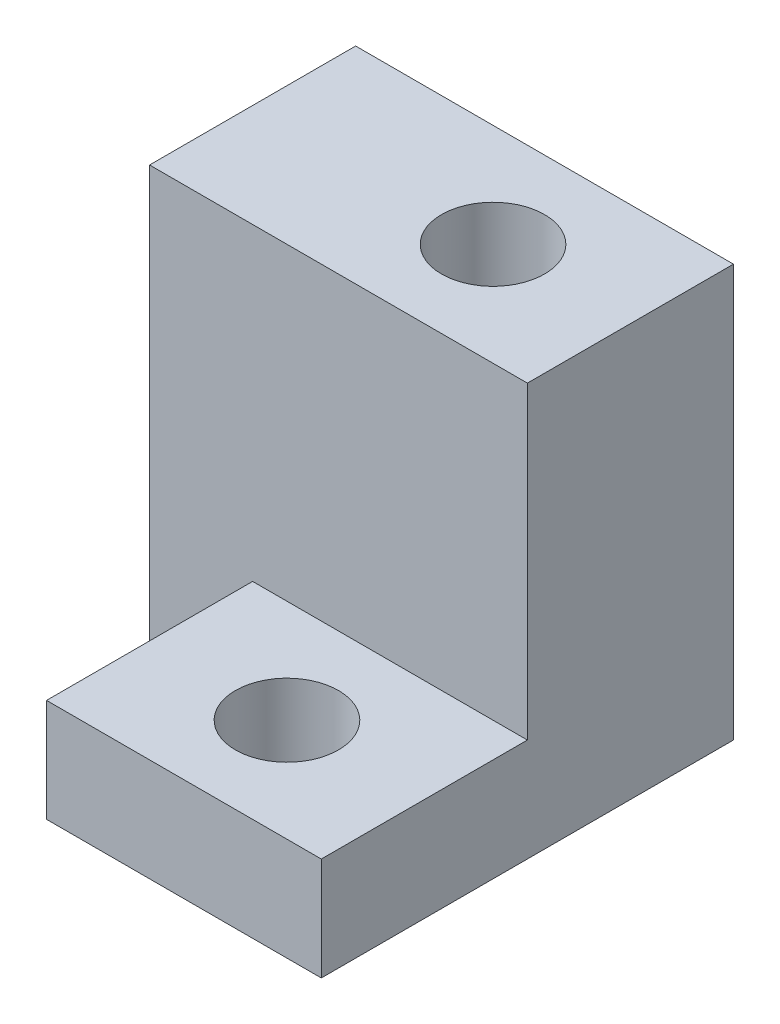
SolidWorks part; units mm, degrees
ref_plane "Front Plane" through (0, 0, 0) normal (0, 0, 1) x (1, 0, 0)
ref_plane "Top Plane" through (0, 0, 0) normal (0, 1, 0) x (1, 0, 0)
ref_plane "Right Plane" through (0, 0, 0) normal (1, 0, 0) x (0, 0, -1)
sketch "Sketch1" plane through (0, 0, 0) normal (0, 0, 1) x (1, 0, 0)
  line L1 (0, 0) -> (11, 0)
  line L2 (0, 0) -> (0, 12)
  line L3 (0, 12) -> (11, 12)
  line L4 (11, 0) -> (11, 12)
  dimension "D1" = 12
  dimension "D2" = 11
extrude "Boss-Extrude1" add sketch "Sketch1" along normal blind 6
sketch "Sketch2" plane through (0, 0, 6) normal (0, 0, 1) x (1, 0, 0)
  line L1 (11, 0) -> (3, 0)
  line L2 (11, 0) -> (11, 3)
  line L3 (11, 3) -> (3, 3)
  line L4 (3, 0) -> (3, 3)
  dimension "D1" = 8
  dimension "D2" = 3
extrude "Boss-Extrude2" add sketch "Sketch2" along normal blind 6
sketch "Sketch3" plane through (0, 3, 0) normal (0, 1, 0) x (1, 0, 0)
  line L0 (11, -12) -> (3, -12) construction
  line L1 (11, -12) -> (11, -6) construction
  circle A0 centre (7, -9) radius 1.5
  dimension "D1" = 3
  dimension "D2" = 3
  dimension "D3" = 4
extrude "Cut-Extrude1" cut sketch "Sketch3" against normal blind 6
sketch "Sketch4" plane through (0, 12, 0) normal (0, 1, 0) x (1, 0, 0)
  line L0 (11, 0) -> (0, 0) construction
  line L1 (11, -6) -> (11, 0) construction
  circle A0 centre (7, -3) radius 1.5
  dimension "D1" = 3
  dimension "D2" = 3
  dimension "D3" = 4
extrude "Cut-Extrude2" cut sketch "Sketch4" against normal blind 16
